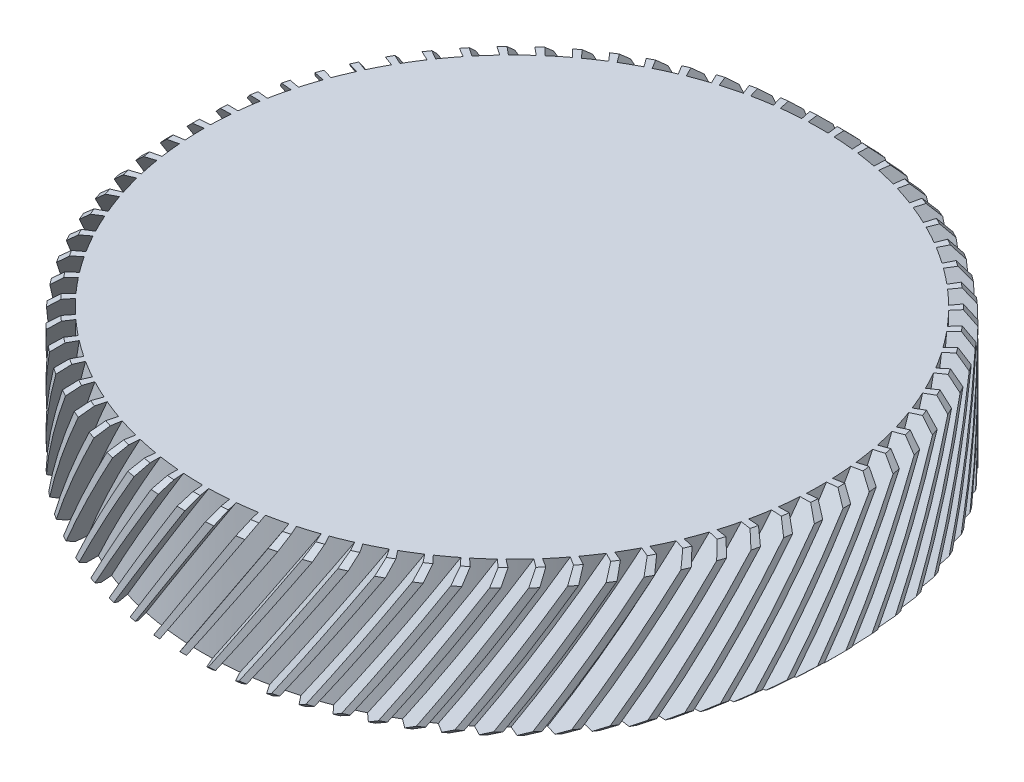
SolidWorks part; units mm, degrees
ref_plane "前视基准面" through (0, 0, 0) normal (0, 0, 1) x (1, 0, 0)
ref_plane "上视基准面" through (0, 0, 0) normal (0, 1, 0) x (1, 0, 0)
ref_plane "右视基准面" through (0, 0, 0) normal (1, 0, 0) x (0, 0, -1)
sketch "草图1" plane through (0, 0, 0) normal (0, 0, 1) x (1, 0, 0)
  line L0 (0, 46.0207) -> (0, -69.6142) construction
  line L1 (13.75, -8.8309) -> (14.35, -8.8309)
  line L2 (15.875, -6.3309) -> (0, -6.3309)
  line L3 (13.75, -13.3309) -> (15.875, -13.3309)
  line L4 (13.75, -13.3309) -> (13.75, -8.8309)
  line L5 (14.35, -8.8309) -> (14.35, -7.8309)
  line L6 (15.875, -13.3309) -> (15.875, -6.3309)
  line L7 (14.35, -7.8309) -> (0, -7.8309)
  line L8 (0, -7.8309) -> (0, -6.3309)
  dimension "D1" = 14.35
  dimension "D2" = 7
  dimension "D3" = 15.875
  dimension "D4" = 13.75
  dimension "D5" = 4.5
  dimension "D6" = 5.5
revolve "旋转1" add sketch "草图1" angle 360 about L0
cosmetic thread "装饰螺纹线1" parameters "D1"=5.5, "D2"=28.5
chamfer "倒角1" distance 0.5 angle 45 2 edges at (0, -6.3309, 15.875) (0, -13.3309, 15.875)
surface "曲面-等距1" parameters "D1"=1
sketch "草图2" plane through (0, 0, 0) normal (0, 0, 1) x (1, 0, 0)
  line L0 (0, -2.7759) -> (-6.5923, -13.3309)
  line L1 (0, -2.7759) -> (0.6785, -3.1997)
  line L2 (-6.5923, -13.3309) -> (-5.9138, -13.7547)
  line L3 (0.6785, -3.1997) -> (-5.9138, -13.7547)
  line L4 (-15.375, -13.3309) -> (15.375, -13.3309) construction
extrude "切除-拉伸1" cut sketch "草图2" against normal up to surface (15.125 mm away) from offset 30
pattern_circular "阵列(圆周)1" count 75 over 360 about axis through (0, 0, 0) along (0, 1, 0) of "切除-拉伸1"
delete or keep bodies "实体-删除/保留 1" type delete bodies bodies 107
